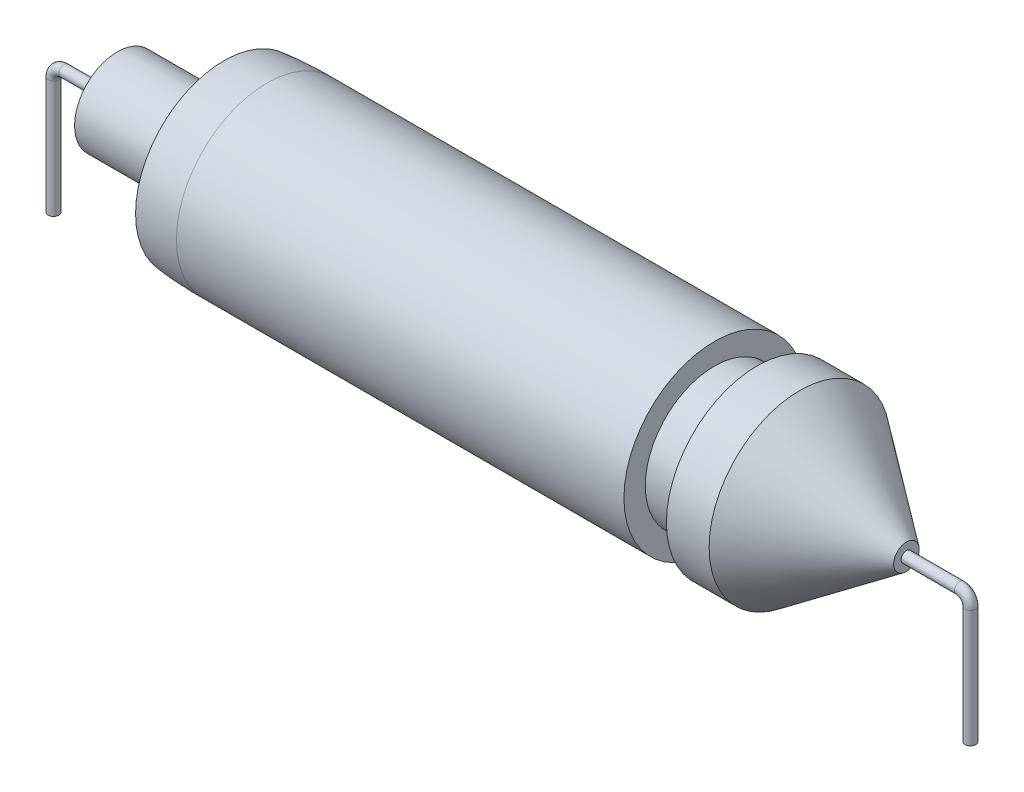
SolidWorks part; units mm, degrees
ref_plane "Front Plane" through (0, 0, 0) normal (0, 0, 1) x (1, 0, 0)
ref_plane "Top Plane" through (0, 0, 0) normal (0, 1, 0) x (1, 0, 0)
ref_plane "Right Plane" through (0, 0, 0) normal (1, 0, 0) x (0, 0, -1)
sketch "Sketch1" plane through (0, 0, 0) normal (0, 1, 0) x (1, 0, 0)
  line L0 (-11120.5684, -4241.4539) -> (9854.0017, -4241.4539)
  line L1 (9854.0017, -4241.4539) -> (9854.0017, -3241.4539)
  line L2 (11854.0017, -4250) -> (11854.0017, -3241.4539)
  line L3 (9854.0017, -3241.4539) -> (11854.0017, -3241.4539)
  line L4 (-13134.9126, -2000) -> (-18134.9126, -2000)
  line L5 (11854.0017, -4250) -> (13854.0017, -4250)
  line L6 (-11145.9983, 4258.5461) -> (9854.0017, 4258.5461)
  line L7 (9854.0017, 4258.5461) -> (9854.0017, 3258.5461)
  line L8 (11854.0017, 4250) -> (11854.0017, 3258.5461)
  line L9 (9854.0017, 3258.5461) -> (11854.0017, 3258.5461)
  line L10 (-18134.9126, -2000) -> (-18134.9126, 2000)
  line L11 (11854.0017, 4250) -> (13854.0017, 4250)
  line L12 (11854.0017, -3241.4539) -> (11854.0017, 3258.5461)
  line L13 (9854.0017, -3241.4539) -> (9854.0017, 3258.5461)
  line L14 (-13134.9126, -4141.9514) -> (-13134.9126, 4158.0486)
  line L15 (-13134.9126, 2000) -> (-18134.9126, 2000)
  line L16 (18854.0017, 0) -> (18854.0017, 600)
  line L17 (18854.0017, -600) -> (18854.0017, 0)
  line L18 (-14850, 0) -> (14850, 0) construction
  line L19 (18854.0017, 600) -> (13854.0017, 4250)
  line L20 (13854.0017, -4250) -> (18854.0017, -600)
  line L21 (-24280.0397, 0) -> (24839.7967, 0) construction
  line L22 (21854.0026, -250) -> (21854.0026, 250)
  line L23 (21854.0026, 250) -> (18854.0026, 250)
  line L24 (21854.0026, -250) -> (18854.0026, -250)
  line L25 (-21134.9126, -250) -> (-21134.9126, 250)
  line L26 (-18134.9126, 250) -> (-21134.9126, 250)
  line L27 (-18134.9126, -250) -> (-21134.9126, -250)
  spline S0 degree 2 poles (-11145.9983, 4258.5461) (-12142.1635, 4267.8297) (-13134.9126, 4158.0486) knots 0 0 0 1 1 1
  spline S1 degree 2 poles (-11120.5684, -4241.4539) (-12129.426, -4249.9871) (-13134.9126, -4141.9514) knots 0 0 0 1 1 1
sketch "Sketch3" plane through (0, 0, 0) normal (0, 0, 1) x (1, 0, 0)
  line L13 (18854.0017, 0) -> (21354.0017, 0)
  line L20 (21854.0017, -500) -> (21854.0017, -6000)
  arc A0 (21854.0017, -500) -> (21354.0017, 0) centre (21354.0017, -500) ccw
  dimension "D1" = 500
sketch "Sketch6" plane through (0, 0, 0) normal (0, 0, 1) x (1, 0, 0)
  line L0 (-18134.9126, 0) -> (-20621.5868, 0)
  line L1 (-21121.5868, -500) -> (-21121.5868, -6000)
  arc A0 (-21121.5868, -500) -> (-20621.5868, 0) centre (-20621.5868, -500) cw
  dimension "D1" = 500
sweep "Sweep7" add path "Sketch3" circular profile diameter 500 parameters "D3"=500
sweep "Sweep8" add path "Sketch6" circular profile diameter 500 parameters "D3"=500
revolve "Revolve2" add sketch "Sketch1" angle 360 about L21
